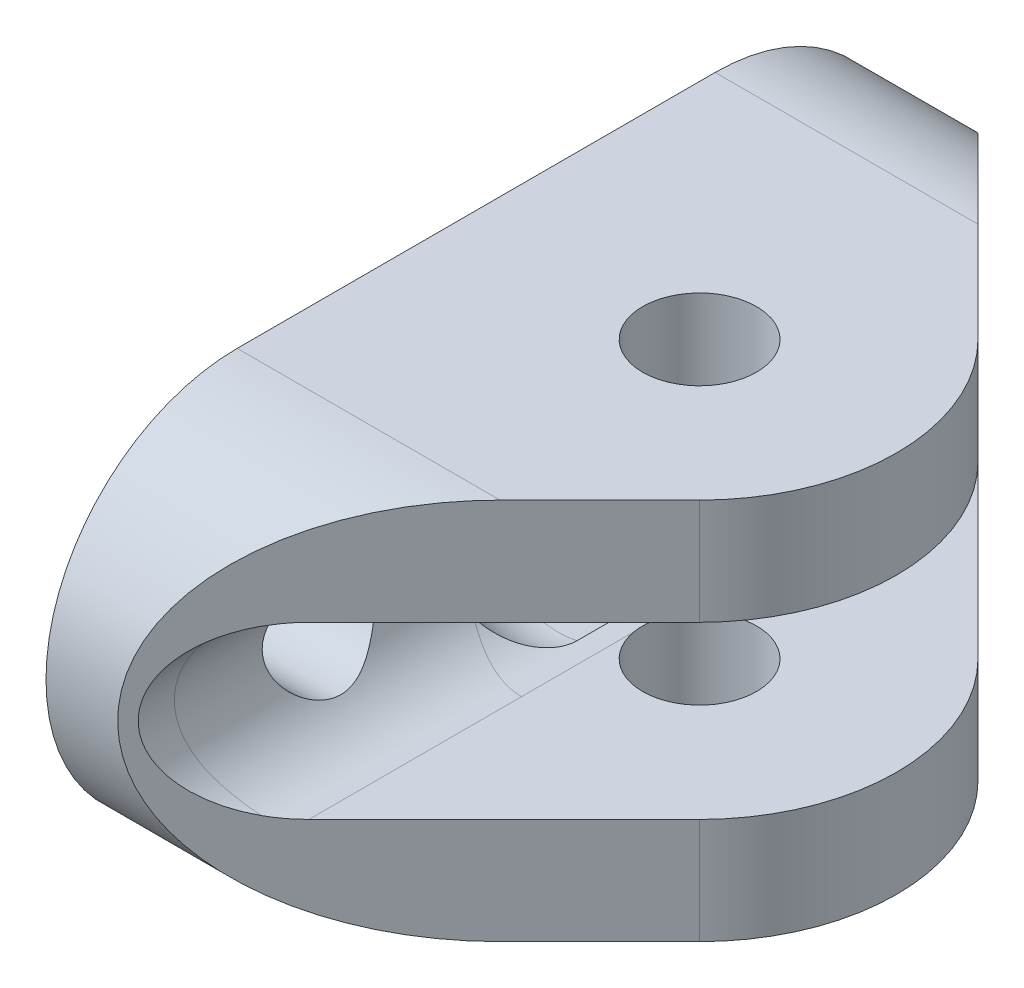
SolidWorks part; units mm, degrees
material "6061-T6 (SS)"
ref_plane "Front Plane" through (0, 0, 0) normal (0, 0, 1) x (1, 0, 0)
ref_plane "Top Plane" through (0, 0, 0) normal (0, 1, 0) x (1, 0, 0)
ref_plane "Right Plane" through (0, 0, 0) normal (1, 0, 0) x (0, 0, -1)
sketch "Sketch1" plane through (0, 0, 0) normal (1, 0, 0) x (0, 0, -1)
  line L0 (20, 16) -> (36, 16) construction
  line L1 (36, 16) -> (36, -16) construction
  line L2 (36, -16) -> (20, -16) construction
  line L3 (-20, 16) -> (0, 16)
  line L4 (-20, -16) -> (0, -16)
  line L5 (0, 0) -> (0, 16) construction
  line L9 (20, 16) -> (0, 16)
  line L10 (20, -16) -> (0, -16)
  circle A0 centre (-20, 0) radius 4.7625
  circle A1 centre (20, 0) radius 4.7625
  arc A2 (-20, 16) -> (-20, -16) centre (-20, 0) ccw
  arc A5 (20, 16) -> (20, -16) centre (20, 0) cw
  dimension "D1" = 9.525
  dimension "D2" = 20
  dimension "D3" = 20
  dimension "D4" = 32
extrude "Boss-Extrude1" add sketch "Sketch1" along normal blind 50
sketch "Sketch3" plane through (0, 0, 0) normal (0, 1, 0) x (1, 0, 0)
  line L0 (6, 36) -> (30.35, 11.65)
  line L1 (0, 0) -> (46.6974, 0) construction
  line L2 (6, -36) -> (30.35, -11.65)
  line L3 (6, 36) -> (6, -36) construction
  line L4 (50, 36) -> (0, 36) construction
  line L5 (30.35, 11.65) -> (42, 0) construction
  line L6 (6, -36) -> (6, -40.7206)
  line L7 (6, -40.7206) -> (53.5379, -40.7206)
  line L8 (53.5379, -40.7206) -> (53.5379, 49.6489)
  line L9 (53.5379, 49.6489) -> (6, 49.6489)
  line L10 (6, 49.6489) -> (6, 36)
  line L11 (30.35, -11.65) -> (42, 0) construction
  arc A0 (30.35, 11.65) -> (30.35, -11.65) centre (18.7, 0) cw
  dimension "D2" = 42
  dimension "D1" = 18.7
extrude "Cut-Extrude3" cut sketch "Sketch3" against normal through all and the other way through all
sketch "Sketch4" plane through (0, 0, 0) normal (0, 1, 0) x (1, 0, 0)
  circle A0 centre (18.7, 0) radius 10
  dimension "D1" = 20
sketch "Sketch5" plane through (0, 0, 0) normal (0, 1, 0) x (1, 0, 0)
  circle A1 centre (18.7, 0) radius 4.7625
  dimension "D2" = 9.525
extrude "Cut-Extrude2" cut sketch "Sketch5" against normal through all and the other way through all
sketch "Sketch7" plane through (0, 0, 0) normal (0, 0, 1) x (1, 0, 0)
  line L0 (56.3512, 0) -> (14, 0) construction
  line L1 (35.1756, -16) -> (35.1756, 16) construction
  line L2 (28.7, 0) -> (8.7, 0) construction
  line L3 (56.3512, -7.1438) -> (14, -7.1438)
  line L4 (56.3512, 7.1437) -> (14, 7.1437)
  arc A0 (56.3512, -7.1438) -> (56.3512, 7.1437) centre (56.3512, 0) ccw
  arc A1 (14, 7.1437) -> (14, -7.1438) centre (14, 0) ccw
  point P6 (35.1756, 0)
  dimension "D1" = 14.2875
  dimension "D2" = 14
extrude "Cut-Extrude4" cut sketch "Sketch7" against normal through all and the other way through all
sketch3d "3DSketch1"
  line L0 (18.7, 0, 0) -> (38.5993, 0, 0) construction
  line L1 (18.7, 0, 0) -> (39.8419, 0, -6.8694)
  line L2 (0, 0, 20) -> (-22.3178, 0, 20) construction
  line L3 (0, 0, -20) -> (-22.7301, 0, -20) construction
  dimension "D1" = 18
fillet "Fillet9" [suppressed] radius 1
fillet "Fillet11" [suppressed] radius 1
sketch "Sketch6" plane through (0, 0, 0) normal (0, 1, 0) x (1, 0, 0)
  line L0 (18.7, 23.4741) -> (18.7, -29.5041) construction
  line L1 (18.7, 0) -> (28.1761, -29.1643)
  line L2 (18.7, 0) -> (11.2483, 22.934)
  dimension "D1" = 18
split line "Split Line1" [suppressed]
ref_plane "Plane1" through (18.7, 0, 0) normal (0.9511, 0, -0.309) x (-0.309, 0, -0.9511)
sketch "Sketch8" plane through (0, 0, 0) normal (1, 0, 0) x (0, 0, -1)
  line L0 (-0.769, -7.1438) -> (-28, -7.1438) construction
  line L1 (-11.65, 7.1437) -> (11.65, 7.1437) construction
  line L2 (-0.769, 7.1437) -> (-28, 7.1437) construction
  line L3 (-29.7909, 7.1437) -> (-10.2091, 7.1437)
  line L4 (-29.7909, -7.1438) -> (-10.2091, -7.1438)
  line L5 (0, 0) -> (0, 23.9608) construction
  line L6 (29.7909, -7.1438) -> (10.2091, -7.1438)
  line L7 (29.7909, 7.1437) -> (10.2091, 7.1437)
  arc A0 (-29.7909, 7.1437) -> (-29.7909, -7.1438) centre (-20, 0) ccw
  arc A1 (-10.2091, -7.1438) -> (-10.2091, 7.1437) centre (-20, 0) ccw
  arc A2 (10.2091, -7.1438) -> (10.2091, 7.1437) centre (20, 0) cw
  arc A3 (29.7909, 7.1437) -> (29.7909, -7.1438) centre (20, 0) cw
  dimension "D1" = 12.12
split line "Split Line2"
sketch "Sketch9" plane through (0, 0, 0) normal (1, 0, 0) x (0, 0, -1)
  circle A0 centre (-20, 0) radius 15
  circle A1 centre (20, 0) radius 15
  dimension "D1" = 30
split line "Split Line3" [suppressed]
sketch "Sketch10" plane through (0, 0, 0) normal (0, 1, 0) x (1, 0, 0)
  line L0 (3.7, 4) -> (3.7, -4)
  line L1 (10.85, 11.15) -> (10.85, -11.15)
  line L2 (3.7, 0) -> (10.85, 0) construction
  arc A0 (10.85, 11.15) -> (3.7, 4) centre (10.85, 4) ccw
  arc A1 (10.85, -11.15) -> (3.7, -4) centre (10.85, -4) cw
  dimension "D1" = 7.15
  dimension "D2" = 15
  dimension "D3" = 4
revolve "Cut-Revolve1" cut sketch "Sketch10" angle 360 about L1
